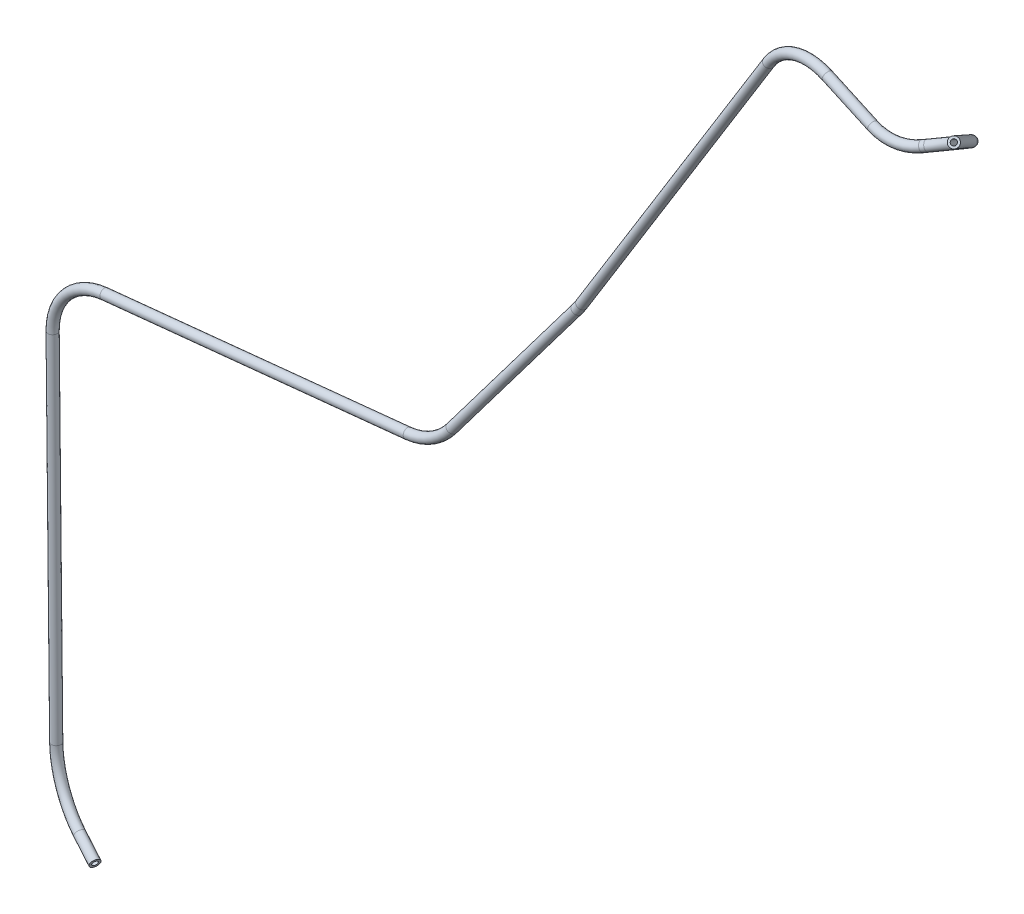
SolidWorks part; units mm, degrees
ref_plane "Płaszczyzna XY" through (0, 0, 0) normal (0, 0, 1) x (1, 0, 0)
ref_plane "Płaszczyzna XZ" through (0, 0, 0) normal (0, 1, 0) x (1, 0, 0)
ref_plane "Płaszczyzna YZ" through (0, 0, 0) normal (1, 0, 0) x (0, 0, -1)
sketch3d "Szkic 3D1"
  line L1 (-22.2076, 528.5225, 141.9247) -> (-56.7827, 538.3672, 137.8613)
  line L2 (-585.1045, 122.1166, 131.4427) -> (-584.9713, -118.6948, 129.1418)
  line L3 (-242.1348, 301.0762, 121.3784) -> (-315.6121, 200.3729, 132.0737)
  line L4 (-343.7428, 184.1435, 133.4708) -> (-549.408, 161.9028, 132.0353)
  line L7 (-101.0949, 521.4667, 133.152) -> (-238.8499, 305.8836, 121.2644)
  line L11 (86.4199, 600.1046, 195.936) -> (51.9622, 560.6322, 150.138)
  line L12 (11.3196, 531.9154, 138.5269) -> (8.6872, 530.7084, 139.3271)
  line L14 (-545.0288, -162.6713, 142.9707) -> (-560.9664, -156.0279, 137.3464)
  arc A0 (-22.2076, 528.5225, 141.9247) -> (8.6872, 530.7084, 139.3271) centre (-10.5319, 561.579, 122.6647) ccw
  arc A2 (-101.0949, 521.4667, 133.152) -> (-56.7827, 538.3672, 137.8613) centre (-67.6726, 499.8824, 137.2836) ccw
  arc A3 (-242.1348, 301.0762, 121.3784) -> (-238.8499, 305.8836, 121.2644) centre (-254.0275, 313.5859, 157.4626) ccw
  arc A5 (-549.408, 161.9028, 132.0353) -> (-585.1045, 122.1166, 131.4427) centre (-545.1052, 122.1365, 131.6808) ccw
  arc A6 (51.9622, 560.6322, 150.138) -> (11.3196, 531.9154, 138.5269) centre (15.2989, 553.3713, 183.9809) ccw
  arc A7 (-584.9713, -118.6948, 129.1418) -> (-560.9664, -156.0279, 137.3464) centre (-547.2992, -118.8025, 142.588) ccw
  arc A8 (-343.7428, 184.1435, 133.4708) -> (-315.6121, 200.3729, 132.0737) centre (-347.9781, 223.6212, 128.6157) ccw
  point P3 (-6.0897, 523.9332, 143.8189)
  point P7 (-9.0037, 581.2969, 157.4335)
  point P11 (-85.1369, 546.4405, 134.5291)
  point P13 (-63.193, 499.2115, 97.5409)
  point P17 (-240.4202, 303.4261, 121.1289)
  point P18 (-223.9151, 293.4116, 174.3812)
  point P27 (37.2872, 543.8215, 130.6334)
  point P28 (-8.6755, 594.2568, 166.7804)
  point P30 (-585.1243, 158.0404, 131.786)
  point P32 (-545.343, 121.7542, 171.6782)
  point P36 (-584.9562, -146.0281, 128.8806)
  point P38 (-560.7459, -119.1699, 180.2583)
  point P48 (-326.0583, 186.0559, 133.5943)
  point P49 (-348.774, 228.4187, 168.319)
  dimension "D2" = 40
  dimension "D3" = 40
  dimension "D1" = 40
  dimension "D4" = 40
ref_plane "Płaszczyzna1" through (86.4199, 600.1046, 195.936) normal (-0.4951, -0.5672, -0.6581) x (-0.8681, 0.3538, 0.3482)
sketch "Szkic1" plane through (86.4199, 600.1046, 195.936) normal (-0.4951, -0.5672, -0.6581) x (-0.8681, 0.3538, 0.3482)
  circle A0 centre (0, 0) radius 1.75
  circle A1 centre (0, 0) radius 3.15
  dimension "D1" = 6.3
  dimension "D2" = 3.5
sweep "Wyciągnięcie po ścieżce1" add profiles "Szkic1" path "Szkic 3D1"
